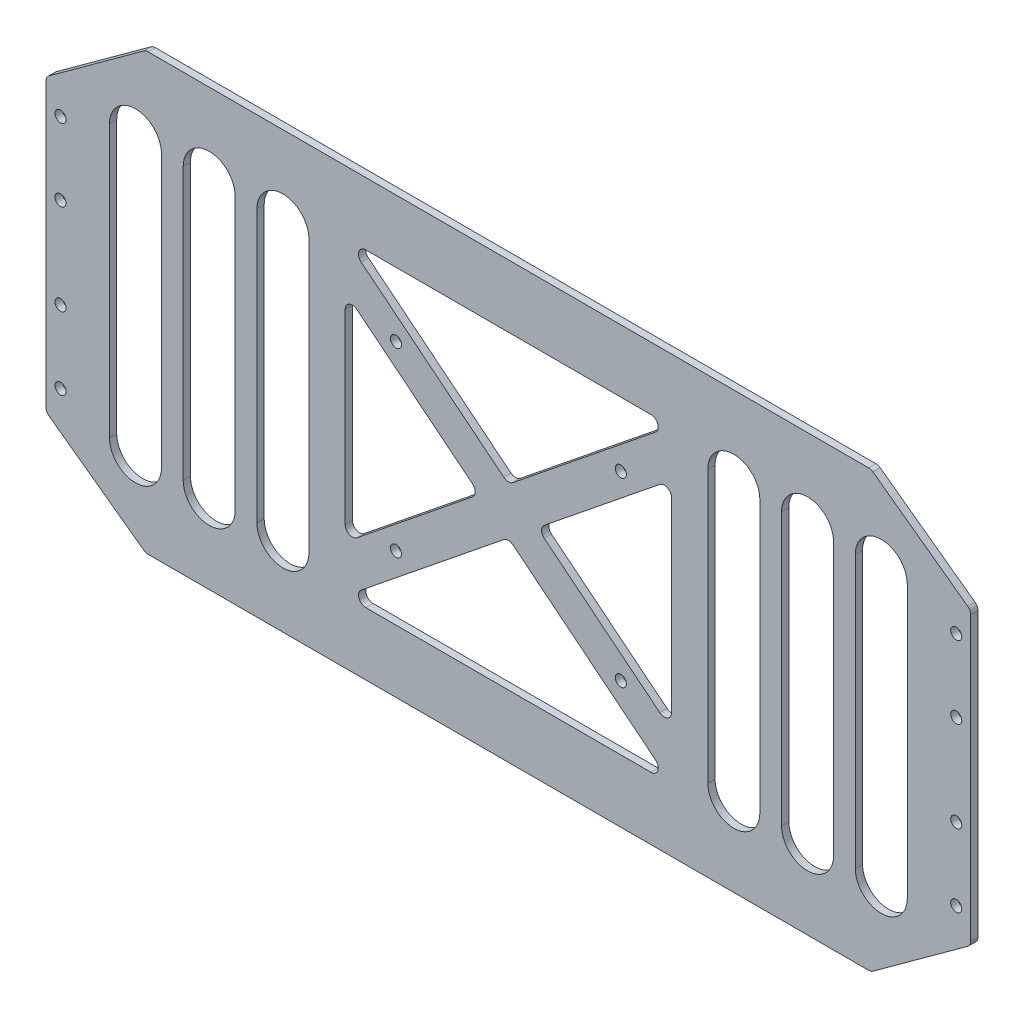
SolidWorks part; units mm, degrees
material "Thornel Mat VMA"
ref_plane "前视基准面" through (0, 0, 0) normal (0, 0, 1) x (1, 0, 0)
ref_plane "上视基准面" through (0, 0, 0) normal (0, 1, 0) x (1, 0, 0)
ref_plane "右视基准面" through (0, 0, 0) normal (1, 0, 0) x (0, 0, -1)
other "Configuration Table"
sketch "草图1" plane through (0, 0, 0) normal (0, 0, 1) x (1, 0, 0)
  line L0 (-100, 60) -> (-127.5, 40)
  line L1 (-100, -60) -> (100, -60)
  line L3 (-100, 60) -> (100, 60)
  line L5 (-100, -60) -> (100, 60) construction
  line L6 (-100, 60) -> (100, -60) construction
  line L7 (-127.5, 40) -> (-127.5, -40)
  line L8 (-127.5, -40) -> (-100, -60)
  line L9 (0, 60) -> (0, 0) construction
  line L10 (127.5, -40) -> (100, -60)
  line L11 (127.5, 40) -> (127.5, -40)
  line L12 (100, 60) -> (127.5, 40)
  point P0 (0, 0)
  dimension "D1" = 255
  dimension "D2" = 120
  dimension "D3" = 80
  dimension "D4" = 200
extrude "凸台-拉伸1" add sketch "草图1" along normal blind 2
sketch "草图2" plane through (0, 0, 0) normal (0, 0, -1) x (-1, 0, 0)
  circle A0 centre (31, -25) radius 1.525
  circle A1 centre (-31, -25) radius 1.525
  circle A2 centre (-31, 25) radius 1.525
  circle A3 centre (31, 25) radius 1.525
  dimension "D1" = 3.05
extrude "切除-拉伸1" cut sketch "草图2" against normal through all both and the other way through all
sketch "草图3" plane through (0, 0, 2) normal (0, 0, 1) x (1, 0, 0)
  line L0 (-127.5, 40) -> (-127.5, -40) construction
  line L1 (0, 0) -> (-127.5, 0) construction
  circle A0 centre (-123.5, -32.5) radius 1.525
  circle A1 centre (-123.5, -12.5) radius 1.525
  circle A2 centre (-123.5, 12.5) radius 1.525
  circle A3 centre (-123.5, 32.5) radius 1.525
  dimension "D1" = 3.05
  dimension "D2" = 4
  dimension "D3" = 20
  dimension "D4" = 20
  dimension "D5" = 25
extrude "切除-拉伸2" cut sketch "草图3" against normal through all both
mirror "镜向1" about plane through (0, 0, 0) normal (1, 0, 0) of "切除-拉伸2"
sketch "草图4" plane through (0, 0, 2) normal (0, 0, 1) x (1, 0, 0)
  line L0 (-45, 42.7136) -> (45, 42.7136)
  line L1 (45, 42.7136) -> (0, 6.4233)
  line L2 (0, 6.4233) -> (-45, 42.7136)
  line L3 (-45, 29.867) -> (-45, -29.867)
  line L4 (-45, -29.867) -> (-7.9649, 0)
  line L5 (-7.9649, 0) -> (-45, 29.867)
  line L6 (-31, 25) -> (0, 0) construction
  line L7 (-31, -25) -> (0, 0) construction
  line L8 (0, 0) -> (-7.9649, 0) construction
  line L9 (0, 0) -> (0, 6.4233) construction
  line L10 (-45, -42.7136) -> (45, -42.7136)
  line L11 (45, -42.7136) -> (0, -6.4233)
  line L12 (0, -6.4233) -> (-45, -42.7136)
  line L13 (45, -29.867) -> (7.9649, 0)
  line L14 (45, 29.867) -> (45, -29.867)
  line L15 (7.9649, 0) -> (45, 29.867)
  point P3 (0, 42.7136)
  point P11 (0, 0)
  dimension "D1" = 90
  dimension "D2" = 5
  dimension "D3" = 5
extrude "切除-拉伸3" cut sketch "草图4" against normal through all both
fillet "圆角1" radius 2 12 edges at (-45, 42.7136, 1) (45, 42.7136, 1) (0, 6.4233, 1) (45, -29.867, 1) (7.9649, 0, 1) (45, 29.867, 1) (-7.9649, 0, 1) (-45, 29.867, 1) (0, -6.4233, 1) (45, -42.7136, 1) (-45, -42.7136, 1) (-45, -29.867, 1)
sketch "草图5" plane through (0, 0, 2) normal (0, 0, 1) x (1, 0, 0)
  line L0 (-102.8333, -37.5) -> (-102.8333, 37.5) construction
  line L1 (-110, -37.5) -> (-110, 37.5)
  line L2 (-95.6667, -37.5) -> (-95.6667, 37.5)
  line L3 (-82.5, 37.5) -> (-82.5, -37.5) construction
  line L4 (-75.3333, 37.5) -> (-75.3333, -37.5)
  line L5 (-89.6667, 37.5) -> (-89.6667, -37.5)
  line L6 (-62.1667, 37.5) -> (-62.1667, -37.5) construction
  line L7 (-55, 37.5) -> (-55, -37.5)
  line L8 (-69.3333, 37.5) -> (-69.3333, -37.5)
  line L9 (-45, 25.6848) -> (-45, -25.6848) construction
  arc A0 (-110, -37.5) -> (-95.6667, -37.5) centre (-102.8333, -37.5) ccw
  arc A1 (-95.6667, 37.5) -> (-110, 37.5) centre (-102.8333, 37.5) ccw
  arc A2 (-75.3333, 37.5) -> (-89.6667, 37.5) centre (-82.5, 37.5) ccw
  arc A3 (-89.6667, -37.5) -> (-75.3333, -37.5) centre (-82.5, -37.5) ccw
  arc A4 (-55, 37.5) -> (-69.3333, 37.5) centre (-62.1667, 37.5) ccw
  arc A5 (-69.3333, -37.5) -> (-55, -37.5) centre (-62.1667, -37.5) ccw
  point P2 (-102.8333, 0)
  point P7 (-82.5, 0)
  point P14 (-62.1667, 0)
  point P23 (-62.6891, -0.2999)
  point P24 (-82.5, 38.5184)
  dimension "D1" = 55
  dimension "D2" = 10
  dimension "D3" = 75
  dimension "D4" = 6
extrude "切除-拉伸4" cut sketch "草图5" against normal through all both
mirror "镜向2" about plane through (0, 0, 0) normal (1, 0, 0) of "切除-拉伸4"
fillet "圆角2" radius 2 8 edges at (127.5, 40, 1) (127.5, -40, 1) (100, -60, 1) (-100, -60, 1) (-127.5, -40, 1) (-127.5, 40, 1) (100, 60, 1) (-100, 60, 1)
